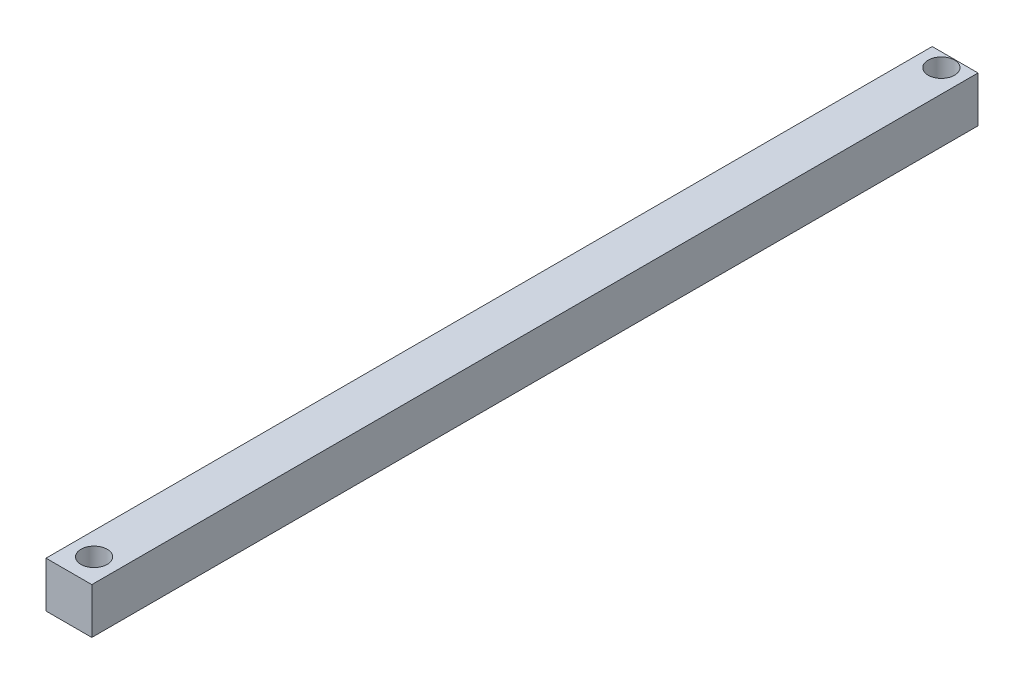
SolidWorks part; units mm, degrees
ref_plane "Front Plane" through (0, 0, 0) normal (0, 0, 1) x (1, 0, 0)
ref_plane "Top Plane" through (0, 0, 0) normal (0, 1, 0) x (1, 0, 0)
ref_plane "Right Plane" through (0, 0, 0) normal (1, 0, 0) x (0, 0, -1)
sketch "Sketch1" plane through (0, 0, 0) normal (0, 1, 0) x (1, 0, 0)
  line L1 (-10, 193.5) -> (10, 193.5)
  line L2 (-10, 193.5) -> (-10, -193.5)
  line L3 (-10, -193.5) -> (10, -193.5)
  line L4 (10, 193.5) -> (10, -193.5)
  line L5 (-10, 193.5) -> (10, -193.5) construction
  line L6 (-10, -193.5) -> (10, 193.5) construction
  point P0 (0, 0)
  dimension "D1" = 20
  dimension "D2" = 387
extrude "Boss-Extrude1" add sketch "Sketch1" along normal blind 20
sketch "Sketch3" plane through (0, 20, 0) normal (0, 1, 0) x (1, 0, 0)
  line L0 (10, 193.5) -> (-10, 193.5) construction
  line L1 (10, -193.5) -> (10, 193.5) construction
  line L2 (0, 187.5) -> (0, -182.5) construction
  circle A0 centre (0, 187.5) radius 5.75
  circle A1 centre (0, -182.5) radius 5.75
  dimension "D1" = 11.5
  dimension "D5" = 11.5
  dimension "D2" = 6
  dimension "D3" = 10
  dimension "D4" = 370
extrude "Cut-Extrude1" cut sketch "Sketch3" against normal through all
